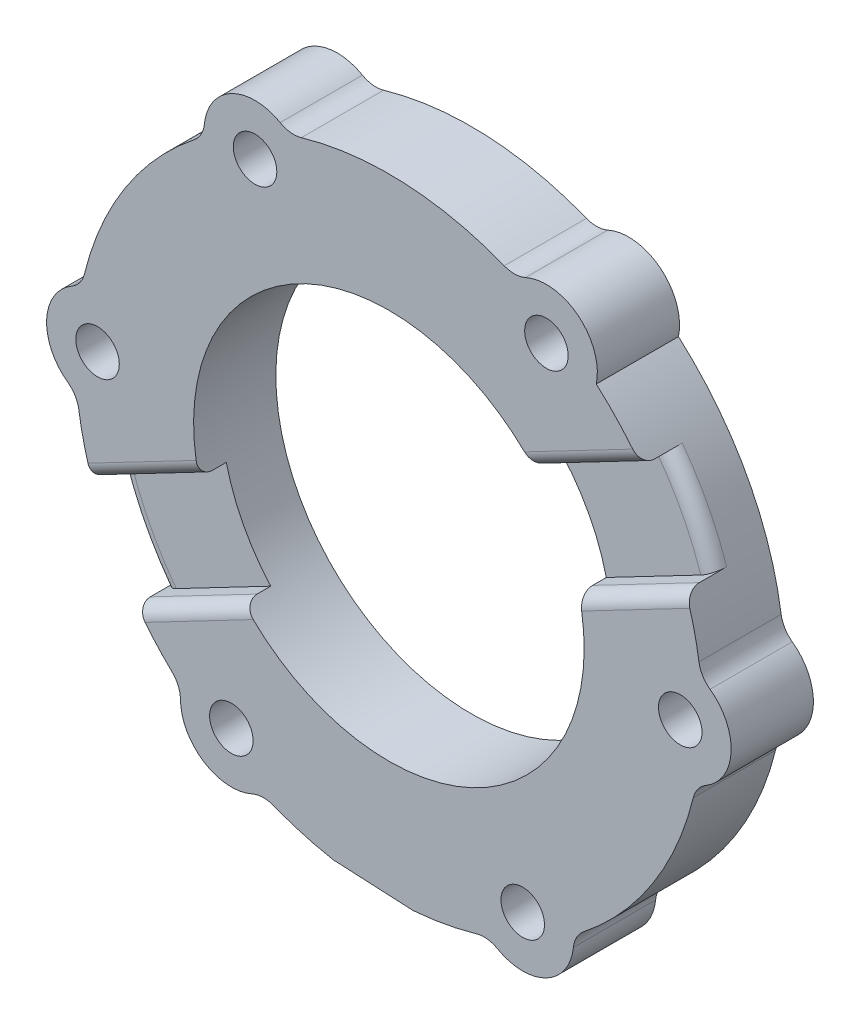
SolidWorks part; units mm, degrees
ref_plane "Front Plane" through (0, 0, 0) normal (0, 0, 1) x (1, 0, 0)
ref_plane "Top Plane" through (0, 0, 0) normal (0, 1, 0) x (1, 0, 0)
ref_plane "Right Plane" through (0, 0, 0) normal (1, 0, 0) x (0, 0, -1)
sketch "Sketch1" plane through (0, 0, 0) normal (0, 0, 1) x (1, 0, 0)
  circle A0 centre (0, 0) radius 14.25
  circle A1 centre (0, 0) radius 25
  dimension "D1" = 28.5
  dimension "D2" = 50
extrude "Boss-Extrude1" add sketch "Sketch1" along normal blind 6
sketch "Sketch2" plane through (0, 0, 6) normal (0, 0, 1) x (1, 0, 0)
  line L0 (-11.6367, -22.1266) -> (9.3514, -23.1852)
  line L1 (-24.3344, -21.4862) -> (22.0875, -23.8275) construction
  circle A0 centre (0, 0) radius 25 construction
  arc A1 (-11.6367, -22.1266) -> (9.3514, -23.1852) centre (0, 0) ccw
extrude "Cut-Extrude1" cut sketch "Sketch2" against normal up to next
sketch "Sketch3" plane through (0, 0, 0) normal (0, 0, -1) x (-1, 0, 0)
  circle A0 centre (9.7657, 18.9113) radius 1.143 construction
  circle A1 centre (9.7657, 18.9113) radius 1.143 construction
  circle A2 centre (-11.4949, 17.913) radius 1.143 construction
  circle A3 centre (-11.4949, 17.913) radius 1.143 construction
  circle A4 centre (-21.2606, -0.9983) radius 1.143 construction
  circle A5 centre (-21.2606, -0.9983) radius 1.143 construction
  circle A6 centre (-9.7657, -18.9113) radius 1.143 construction
  circle A7 centre (-9.7657, -18.9113) radius 1.143 construction
  circle A8 centre (11.4949, -17.913) radius 1.143 construction
  circle A9 centre (11.4949, -17.913) radius 1.143 construction
  circle A10 centre (21.2606, 0.9983) radius 1.143 construction
  circle A11 centre (21.2606, 0.9983) radius 1.143 construction
  circle A12 centre (11.4949, -17.913) radius 1.5875
  circle A13 centre (21.2606, 0.9983) radius 1.5875
  circle A14 centre (9.7657, 18.9113) radius 1.5875
  circle A15 centre (-11.4949, 17.913) radius 1.5875
  circle A16 centre (-21.2606, -0.9983) radius 1.5875
  circle A17 centre (-9.7657, -18.9113) radius 1.5875
  dimension "D1" = 3.175
extrude "Cut-Extrude2" cut sketch "Sketch3" against normal up to next
sketch "Sketch4" plane through (0, 0, 6) normal (0, 0, 1) x (1, 0, 0)
  line L0 (15.802, 4.3065) -> (12.5607, 10.5108) construction
  line L1 (15.802, 4.3065) -> (12.5607, 10.5108) construction
  line L2 (12.5607, 10.5108) -> (35.0259, 22.2471)
  line L3 (35.0259, 22.2471) -> (38.2672, 16.0428)
  line L4 (15.802, 4.3065) -> (38.2672, 16.0428)
  line L5 (12.5607, 10.5108) -> (-54.4326, -24.4879)
  line L6 (15.802, 4.3065) -> (-51.1913, -30.6923)
  line L7 (-54.4326, -24.4879) -> (-51.1913, -30.6923)
extrude "Cut-Extrude3" cut sketch "Sketch4" against normal blind 2
sketch "Sketch5" plane through (0, 0, 6) normal (0, 0, 1) x (1, 0, 0)
  arc A0 (-7.9314, 22.1431) -> (-13.4627, 19.2867) centre (-9.7657, 18.9113) ccw
  arc A1 (-14.2099, 17.9216) -> (-22.2125, 5.4508) centre (0, 0) ccw
  arc A2 (15.1318, 17.1503) -> (9.9714, 21.3024) centre (11.4949, 17.913) ccw
  arc A3 (23.1421, -4.2028) -> (23.4341, 2.0157) centre (21.2606, -0.9983) ccw
  arc A4 (7.9314, -22.1431) -> (13.4627, -19.2867) centre (9.7657, -18.9113) ccw
  arc A5 (-15.2108, -17.9403) -> (-9.9714, -21.3024) centre (-11.4949, -17.913) ccw
  arc A6 (-23.1421, 4.2028) -> (-23.4341, -2.0157) centre (-21.2606, 0.9983) ccw
  arc A7 (8.4156, 21.2669) -> (-6.3857, 21.962) centre (0, 0) ccw
  arc A8 (22.6255, 3.3453) -> (15.1318, 17.1503) centre (0, 0) ccw
  arc A9 (14.2099, -17.9216) -> (22.2125, -5.4508) centre (0, 0) ccw
  arc A10 (-8.4156, -21.2669) -> (6.3857, -21.962) centre (0, 0) ccw
  arc A11 (-22.6255, -3.3453) -> (-15.8268, -16.5112) centre (0, 0) ccw
  circle A12 centre (0, 0) radius 41.7683
  arc A13 (23.1421, -4.2028) -> (22.2125, -5.4508) centre (24.1548, -5.9274) ccw
  arc A14 (23.4341, 2.0157) -> (22.6255, 3.3453) centre (24.604, 3.6379) cw
  arc A15 (9.9714, 21.3024) -> (8.4156, 21.2669) centre (9.1515, 23.1266) cw
  arc A16 (-7.9314, 22.1431) -> (-6.3857, 21.962) centre (-6.9441, 23.8824) ccw
  arc A17 (-13.4627, 19.2867) -> (-14.2099, 17.9216) centre (-15.4525, 19.4888) cw
  arc A18 (-23.1421, 4.2028) -> (-22.2125, 5.4508) centre (-24.1548, 5.9274) ccw
  arc A19 (7.9314, -22.1431) -> (6.3857, -21.962) centre (6.9441, -23.8824) ccw
  arc A20 (-9.9714, -21.3024) -> (-8.4156, -21.2669) centre (-9.1515, -23.1266) cw
  arc A21 (-15.2108, -17.9403) -> (-15.8268, -16.5112) centre (-17.2107, -17.955) ccw
  arc A22 (-23.4341, -2.0157) -> (-22.6255, -3.3453) centre (-24.604, -3.6379) cw
  arc A23 (13.4627, -19.2867) -> (14.2099, -17.9216) centre (15.4525, -19.4888) cw
  point P24 (0, 0)
  dimension "D2" = 2
  dimension "D3" = 2
  dimension "D1" = 6
extrude "Cut-Extrude4" cut sketch "Sketch5" against normal up to next
fillet "Fillet1" radius 1 6 edges at (20.2718, 10.5904, 4) (-20.2718, -10.5904, 4) (-14.5176, -11.5331, 6) (17.7589, 5.3288, 6) (14.5176, 11.5331, 6) (-17.7589, -5.3288, 6)
